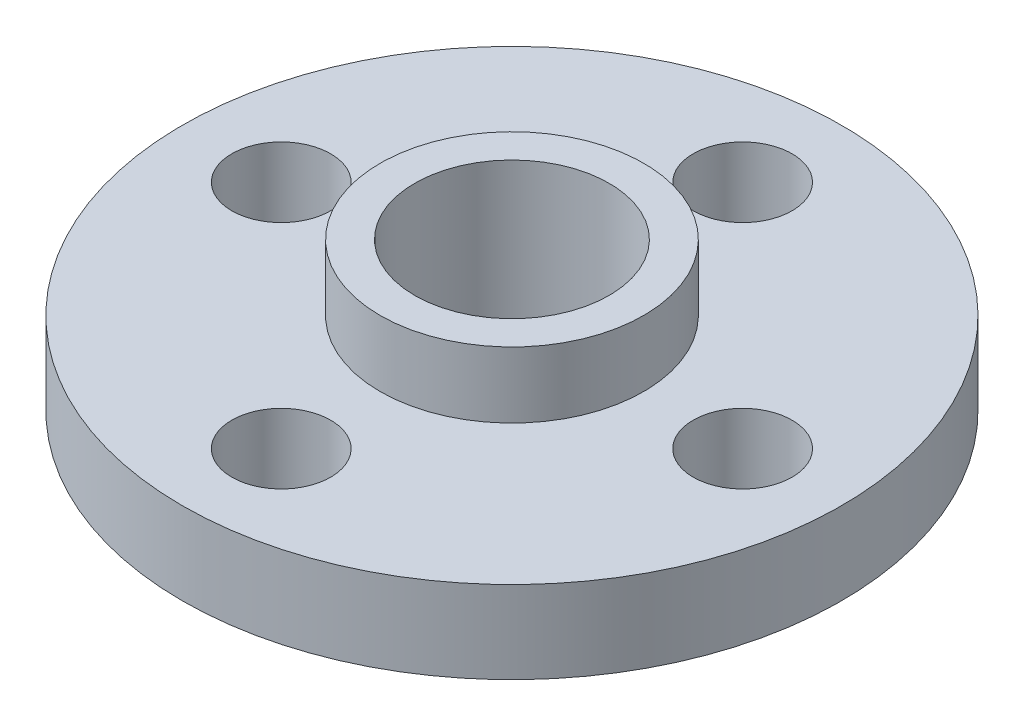
SolidWorks part; units mm, degrees
material "1060 Сплав"
ref_plane "Спереди" through (0, 0, 0) normal (0, 0, 1) x (1, 0, 0)
ref_plane "Сверху" through (0, 0, 0) normal (0, 1, 0) x (1, 0, 0)
ref_plane "Справа" through (0, 0, 0) normal (1, 0, 0) x (0, 0, -1)
sketch "Эскиз1" plane through (0, 0, 0) normal (0, 1, 0) x (1, 0, 0)
  circle A0 centre (0, 0) radius 10
  circle A1 centre (-7, 0) radius 1.5
  circle A2 centre (0, 7) radius 1.5
  circle A3 centre (0, -7) radius 1.5
  circle A4 centre (7, 0) radius 1.5
  circle A5 centre (0, 0) radius 2.95
  dimension "D1" = 20
  dimension "D2" = 3
  dimension "D3" = 3
  dimension "D4" = 3
  dimension "D5" = 3
  dimension "D10" = 5.9
  dimension "D6" = 7
  dimension "D7" = 14
  dimension "D8" = 7
  dimension "D9" = 14
extrude "Бобышка-Вытянуть1" add sketch "Эскиз1" along normal blind 2.5
sketch "Эскиз2" plane through (0, 2.5, 0) normal (0, 1, 0) x (1, 0, 0)
  circle A0 centre (0, 0) radius 2.95
  circle A1 centre (0, 0) radius 4
  dimension "D1" = 8
extrude "Бобышка-Вытянуть2" add sketch "Эскиз2" along normal blind 2
